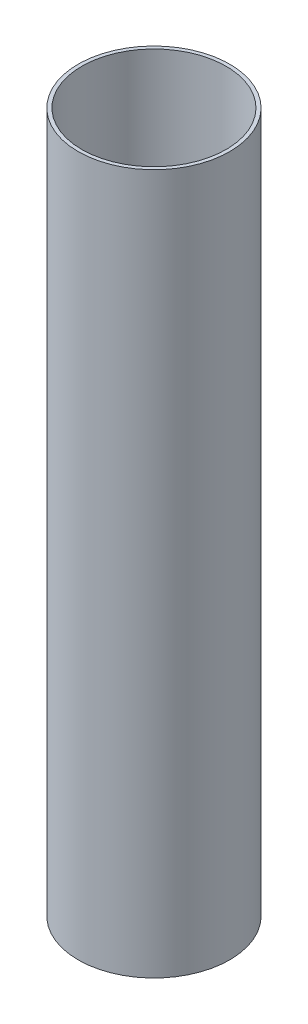
SolidWorks part; units mm, degrees
ref_plane "Front Plane" through (0, 0, 0) normal (0, 0, 1) x (1, 0, 0)
ref_plane "Top Plane" through (0, 0, 0) normal (0, 1, 0) x (1, 0, 0)
ref_plane "Right Plane" through (0, 0, 0) normal (1, 0, 0) x (0, 0, -1)
sketch "Sketch1" plane through (0, 0, 0) normal (0, 1, 0) x (1, 0, 0)
  circle A0 centre (0, 0) radius 20
  circle A1 centre (0, 0) radius 21
extrude "Boss-Extrude2" add sketch "Sketch1" along normal blind 194
